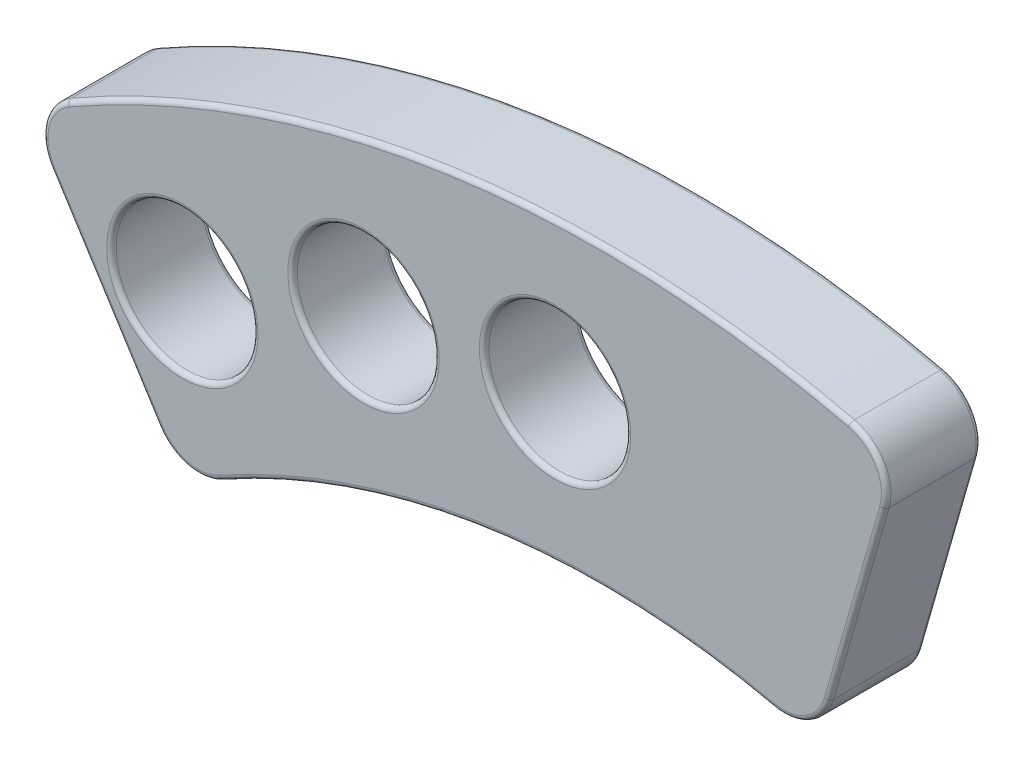
SolidWorks part; units mm, degrees
ref_plane "Piano frontale" through (0, 0, 0) normal (0, 0, 1) x (1, 0, 0)
ref_plane "Piano superiore" through (0, 0, 0) normal (0, 1, 0) x (1, 0, 0)
ref_plane "Piano destro" through (0, 0, 0) normal (1, 0, 0) x (0, 0, -1)
sketch "Schizzo2" plane through (0, 0, 0) normal (0, 0, 1) x (1, 0, 0)
  line L0 (9.6229, 33.5957) -> (11.9666, 41.7778)
  line L13 (-18.7272, 29.5054) -> (-23.2877, 36.6917)
  arc A14 (-16.0651, 28.83) -> (-18.7272, 29.5054) centre (-17.0385, 30.5771) cw
  arc A19 (-23.2877, 36.6917) -> (-22.5919, 39.4995) centre (-21.599, 37.7633) cw
  arc A27 (10.5057, 44.2745) -> (-22.592, 39.4994) centre (0, 0) ccw
  arc A28 (7.2603, 32.1954) -> (-16.0651, 28.83) centre (0, 0) ccw
  arc A29 (7.2603, 32.1954) -> (9.6229, 33.5957) centre (7.7003, 34.1464) ccw
  arc A30 (11.9666, 41.7778) -> (10.5057, 44.2745) centre (10.0439, 42.3286) ccw
  circle A32 centre (-17.7126, 34.9726) radius 3
  circle A33 centre (-10.0544, 37.891) radius 3
  circle A34 centre (-1.9567, 39.1534) radius 3
  point P19 (0, 0)
  dimension "D1" = 2
  dimension "D2" = 2
  dimension "D3" = 3
extrude "Estrusione-Estrusione3" add sketch "Schizzo2" along normal blind 4 contours L0 A30 A27 A19 L13 A14 A28 A29 A34 A33 A32
fillet "Raccordo2" radius 0.2 22 edges at (8.72, 32.4259, 4) (-4.713, 32.6656, 4) (-17.5304, 28.6385, 4) (-21.0074, 33.0986, 4) (-23.5403, 38.2444, 4) (-6.4977, 45.0376, 4) (11.7701, 43.3386, 4) (10.7948, 37.6868, 4) (-14.7126, 34.9726, 4) (-7.0544, 37.891, 4) (1.0433, 39.1534, 4) (11.7701, 43.3386, 0) (-6.4977, 45.0376, 0) (-23.5403, 38.2444, 0) (-21.0074, 33.0986, 0) (-17.5304, 28.6385, 0) (-4.713, 32.6656, 0) (8.72, 32.4259, 0) (10.7948, 37.6868, 0) (-14.7126, 34.9726, 0) (-7.0544, 37.891, 0) (1.0433, 39.1534, 0)
